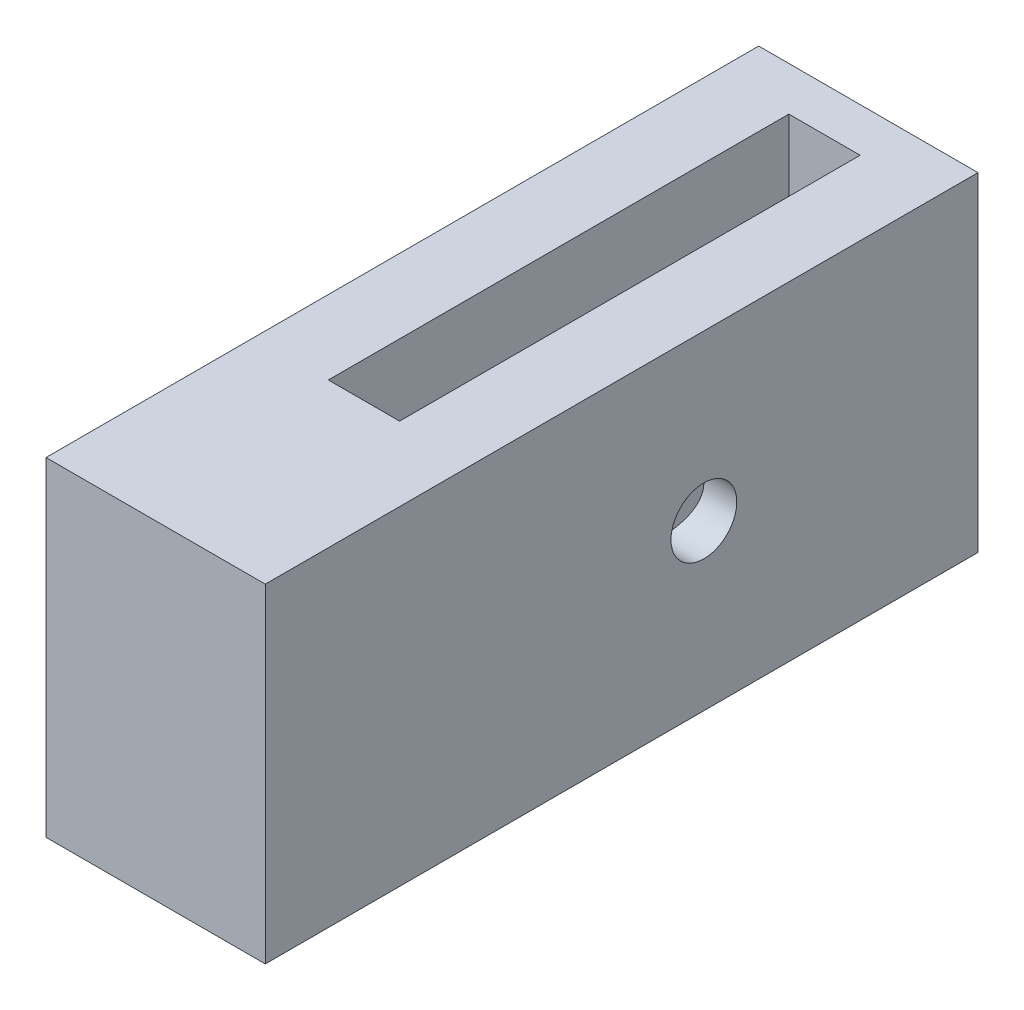
SolidWorks part; units mm, degrees
ref_plane "Front Plane" through (0, 0, 0) normal (0, 0, 1) x (1, 0, 0)
ref_plane "Top Plane" through (0, 0, 0) normal (0, 1, 0) x (1, 0, 0)
ref_plane "Right Plane" through (0, 0, 0) normal (1, 0, 0) x (0, 0, -1)
sketch "Sketch1" plane through (0, 0, 0) normal (0, 0, 1) x (1, 0, 0)
  line L5 (-10, -15) -> (10, -15)
  line L6 (-10, -15) -> (-10, 15)
  line L7 (-10, 15) -> (10, 15)
  line L8 (10, -15) -> (10, 15)
  line L9 (-10, -15) -> (10, 15) construction
  line L10 (-10, 15) -> (10, -15) construction
  point P0 (0, 0)
  dimension "D1" = 20
  dimension "D2" = 30
extrude "Boss-Extrude1" add sketch "Sketch1" along normal blind 65
sketch "Sketch3" plane through (0, 0, 0) normal (0, 0, 1) x (1, 0, 0)
  circle A0 centre (0, 0) radius 7
  dimension "D1" = 14
extrude "Cut-Extrude1" cut sketch "Sketch3" along normal blind 60
sketch "Sketch4" plane through (-10, 0, 0) normal (-1, 0, 0) x (0, 0, 1)
  circle A0 centre (25, 0) radius 3
  dimension "D1" = 25
  dimension "D2" = 6
  dimension "D3" = 0
extrude "Cut-Extrude2" cut sketch "Sketch4" against normal through all
sketch "Sketch5" plane through (0, 15, 0) normal (0, 1, 0) x (1, 0, 0)
  line L1 (-3.25, -46) -> (3.25, -46)
  line L2 (-3.25, -46) -> (-3.25, -4)
  line L3 (-3.25, -4) -> (3.25, -4)
  line L4 (3.25, -46) -> (3.25, -4)
  line L5 (-3.25, -46) -> (3.25, -4) construction
  line L6 (-3.25, -4) -> (3.25, -46) construction
  point P0 (0, -25)
  dimension "D1" = 25
  dimension "D2" = 42
  dimension "D3" = 0
  dimension "D4" = 6.5
extrude "Cut-Extrude3" cut sketch "Sketch5" against normal through all
